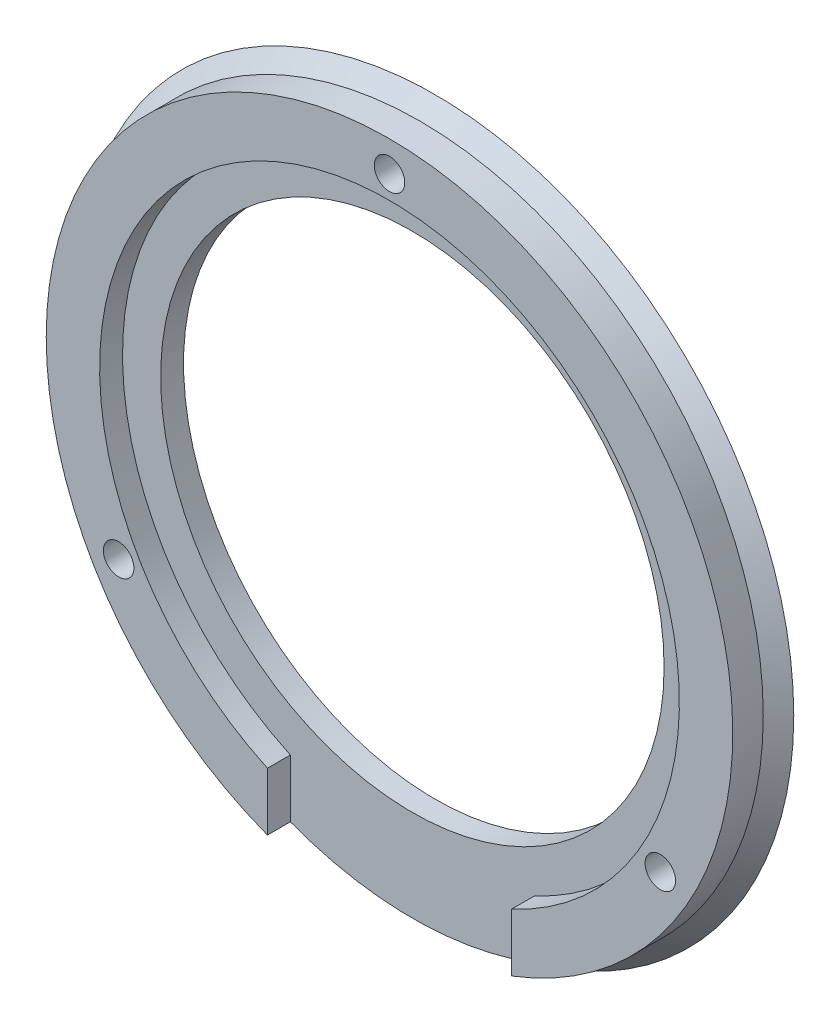
SolidWorks part; units mm, degrees
ref_plane "前视基准面" through (0, 0, 0) normal (0, 0, 1) x (1, 0, 0)
ref_plane "上视基准面" through (0, 0, 0) normal (0, 1, 0) x (1, 0, 0)
ref_plane "右视基准面" through (0, 0, 0) normal (1, 0, 0) x (0, 0, -1)
sketch "草图1" plane through (0, 0, 0) normal (0, 0, 1) x (1, 0, 0)
  circle A0 centre (0, 0) radius 16.5
  circle A1 centre (0, 0) radius 25
extrude "凸台-拉伸1" add sketch "草图1" along normal blind 3
sketch "草图2" plane through (0, 0, 3) normal (0, 0, 1) x (1, 0, 0)
  circle A0 centre (0, 0) radius 19
extrude "切除-拉伸1" cut sketch "草图2" against normal blind 1.5
sketch "草图3" plane through (0, 0, 3) normal (0, 0, 1) x (1, 0, 0)
  line L6 (0, -29.9862) -> (8, -29.9862)
  line L7 (8, -29.9862) -> (8, -6.3788)
  line L8 (8, -6.3788) -> (-8, -6.3788)
  line L9 (-8, -6.3788) -> (-8, -29.9862)
  line L10 (-8, -29.9862) -> (0, -29.9862)
extrude "切除-拉伸2" cut sketch "草图3" against normal blind 1.5
sketch "草图4" plane through (0, 0, 3) normal (0, 0, 1) x (1, 0, 0)
  line L1 (0, 0) -> (0, 20.5) construction
  circle A2 centre (0, 20.5) radius 1
  circle A3 centre (17.7535, -10.25) radius 1
  circle A4 centre (-17.7535, -10.25) radius 1
  dimension "D1" = 3
  dimension "D2" = 20.5
extrude "切除-拉伸3" cut sketch "草图4" against normal blind 31.5
sketch "草图6" plane through (0, 0, 0) normal (0, 0, -1) x (-1, 0, 0)
  line L0 (0, 0) -> (0, 20.5) construction
  circle A0 centre (0, 20.5) radius 1.5
  circle A1 centre (17.7535, -10.25) radius 1.5
  circle A2 centre (-17.7535, -10.25) radius 1.5
  dimension "D1" = 3
  dimension "D2" = 20.5
extrude "切除-拉伸4" cut sketch "草图6" against normal blind 1
sketch "草图8" plane through (0, 0, 0) normal (0, 1, 0) x (1, 0, 0)
  line L0 (0, 0) -> (0, -3)
  line L1 (-25, -3) -> (25, -3) construction
  line L8 (-22.5, -1) -> (-22.5, -3)
  line L11 (-24, 1.038) -> (-26.3307, 1.038)
  line L12 (-26.3307, 1.038) -> (-26.3307, -3)
  line L13 (-22.5, -3) -> (-22.5, -4.2212)
  line L14 (-22.5, -4.2212) -> (-26.3307, -4.2212)
  line L15 (-26.3307, -4.2212) -> (-26.3307, -3)
  line L16 (0, 0) -> (-23.5, 0)
  line L17 (25, 0) -> (-25, 0) construction
  line L18 (-22.5, -1) -> (-23.5, 0)
  line L19 (-23.5, 0) -> (-23.5, 1.038)
  line L20 (-23.5, 1.038) -> (-24, 1.038)
revolve "切除-旋转1" cut sketch "草图8" angle 360 about L0
